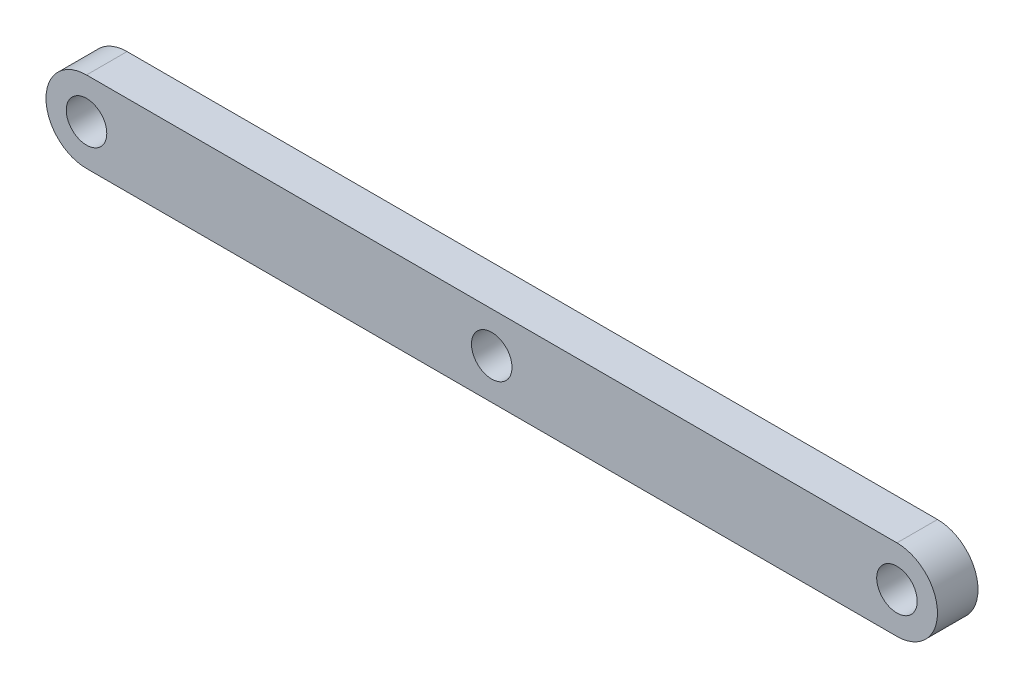
SolidWorks part; units mm, degrees
ref_plane "Front" through (0, 0, 0) normal (0, 0, 1) x (1, 0, 0)
ref_plane "Top" through (0, 0, 0) normal (0, 1, 0) x (1, 0, 0)
ref_plane "Right" through (0, 0, 0) normal (1, 0, 0) x (0, 0, -1)
sketch "草图2" plane through (0, 0, 0) normal (0, 0, 1) x (1, 0, 0)
  line L0 (0, 0) -> (200, 0) construction
  line L1 (0, 10) -> (200, 10)
  line L2 (0, -10) -> (200, -10)
  arc A0 (0, 10) -> (0, -10) centre (0, 0) ccw
  arc A1 (200, -10) -> (200, 10) centre (200, 0) ccw
  circle A2 centre (0, 0) radius 5
  circle A3 centre (200, 0) radius 5
  circle A4 centre (100, 0) radius 5
  point P3 (100, 0)
  dimension "D2" = 10
  dimension "D3" = 10
  dimension "D4" = 10
  dimension "D5" = 10
  dimension "D1" = 200
extrude "凸台-拉伸1" add sketch "草图2" along normal blind 10
